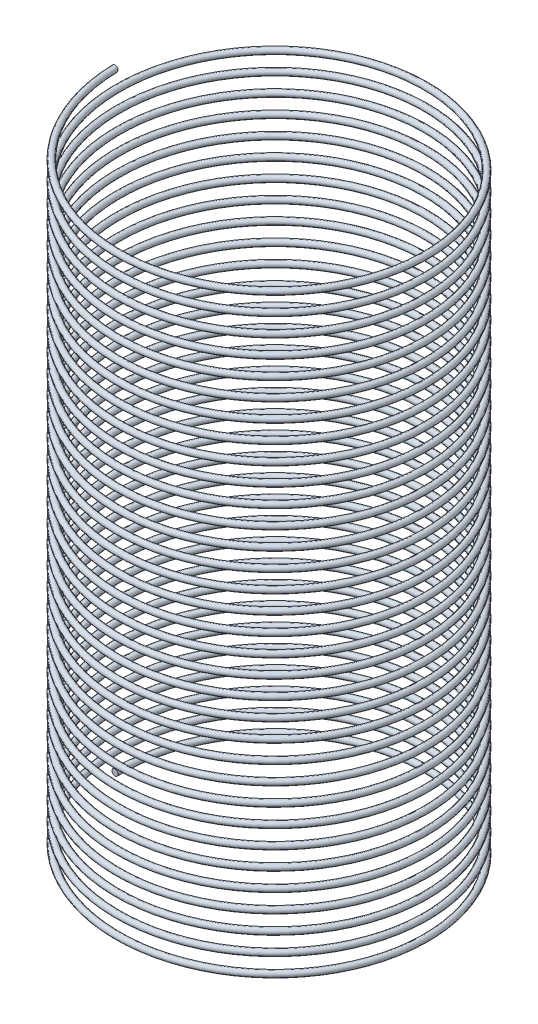
SolidWorks part; units mm, degrees
ref_plane "Front Plane" through (0, 0, 0) normal (0, 0, 1) x (1, 0, 0)
ref_plane "Top Plane" through (0, 0, 0) normal (0, 1, 0) x (1, 0, 0)
ref_plane "Right Plane" through (0, 0, 0) normal (1, 0, 0) x (0, 0, -1)
sketch "Sketch3" plane through (0, 0, 0) normal (0, 1, 0) x (1, 0, 0)
  circle A0 centre (0, 0) radius 25
  dimension "D1" = 50
curve "Helix/Spiral2" pitch 3 height 99 turns 33
sketch "Sketch4" plane through (0, 0, 0) normal (0, 0, 1) x (1, 0, 0)
  circle A0 centre (-25, 0) radius 0.5
  spline S0 degree 3 poles (-25, 0) (-25, 0.0451) (-24.3232, 0.1357) (-21.3588, 0.2712) (-16.6829, 0.4069) (-10.67, 0.5425) (-3.8022, 0.6781) (3.3704, 0.8137) (10.2728, 0.9493) (16.3521, 1.0849) (21.121, 1.2205) (24.1973, 1.3562) (25.3347, 1.4918) (24.4418, 1.6274) (21.5903, 1.763) (17.0087, 1.8986) (11.064, 2.0342) (4.2328, 2.1699) (-2.9376, 2.3055) (-9.8726, 2.4411) (-16.0165, 2.5767) (-20.8769, 2.7123) (-24.0643, 2.8479) (-25.3234, 2.9836) (-24.5532, 3.1192) (-21.8154, 3.2548) (-17.3294, 3.3904) (-11.4548, 3.526) (-4.6622, 3.6616) (2.5039, 3.7973) (9.4695, 3.9329) (15.6762, 4.0685) (20.6266, 4.2041) (23.9242, 4.3397) (25.3046, 4.4753) (24.6573, 4.611) (22.034, 4.7466) (17.6451, 4.8822) (11.8421, 5.0178) (5.0902, 5.1534) (-2.0696, 5.289) (-9.0635, 5.4247) (-15.3312, 5.5603) (-20.3703, 5.6959) (-23.777, 5.8315) (-25.2784, 5.9671) (-24.7541, 6.1027) (-22.2461, 6.2384) (-17.9555, 6.374) (-12.226, 6.5096) (-5.5168, 6.6452) (1.6345, 6.7808) (8.6549, 6.9164) (14.9816, 7.0521) (20.1078, 7.1877) (23.6227, 7.3233) (25.2446, 7.4589) (24.8435, 7.5945) (22.4516, 7.7301) (18.2606, 7.8658) (12.6062, 8.0014) (5.9416, 8.137) (-1.199, 8.2726) (-8.2437, 8.4082) (-14.6277, 8.5438) (-19.8395, 8.6795) (-23.4615, 8.8151) (-25.2034, 8.9507) (-24.9256, 9.0863) (-22.6505, 9.2219) (-18.5602, 9.3575) (-12.9827, 9.4932) (-6.3648, 9.6288) (0.7632, 9.7644) (7.83, 9.9) (14.2693, 10.0356) (19.5652, 10.1712) (23.2932, 10.3068) (25.1547, 10.4425) (25.0003, 10.5781) (22.8426, 10.7137) (18.8544, 10.8493) (13.3553, 10.9849) (6.786, 11.1205) (-0.3271, 11.2562) (-7.414, 11.3918) (-13.9068, 11.5274) (-19.2852, 11.663) (-23.1181, 11.7986) (-25.0985, 11.9342) (-25.0677, 12.0699) (-23.028, 12.2055) (-19.143, 12.3411) (-13.724, 12.4767) (-7.2052, 12.6123) (-0.109, 12.7479) (6.9959, 12.8836) (13.5402, 13.0192) (18.9994, 13.1548) (22.9362, 13.2904) (25.0349, 13.426) (25.1275, 13.5616) (23.2065, 13.6973) (19.4259, 13.8329) (14.0886, 13.9685) (7.6223, 14.1041) (0.5452, 14.2397) (-6.5756, 14.3753) (-13.1695, 14.511) (-18.708, 14.6466) (-22.7474, 14.7822) (-24.9639, 14.9178) (-25.18, 15.0534) (-23.3782, 15.189) (-19.7031, 15.3247) (-14.449, 15.4603) (-8.0371, 15.5959) (-0.9812, 15.7315) (6.1534, 15.8671) (12.7949, 16.0027) (18.4111, 16.1384) (22.5519, 16.274) (24.8855, 16.4096) (25.2249, 16.5452) (23.543, 16.6808) (19.9744, 16.8164) (14.8052, 16.9521) (8.4496, 17.0877) (1.4168, 17.2233) (-5.7294, 17.3589) (-12.4165, 17.4945) (-18.1087, 17.6301) (-22.3497, 17.7658) (-24.7997, 17.9014) (-25.2624, 18.037) (-23.7007, 18.1726) (-20.2398, 18.3082) (-15.157, 18.4438) (-8.8595, 18.5795) (-1.8521, 18.7151) (5.3037, 18.8507) (12.0345, 18.9863) (17.8009, 19.1219) (22.1409, 19.2575) (24.7066, 19.3932) (25.2924, 19.5288) (23.8515, 19.6644) (20.4992, 19.8) (15.5042, 19.9356) (9.2668, 20.0712) (2.2868, 20.2068) (-4.8764, 20.3425) (-11.6489, 20.4781) (-17.4879, 20.6137) (-21.9255, 20.7493) (-24.6061, 20.8849) (-25.315, 21.0205) (-23.9952, 21.1562) (-20.7525, 21.2918) (-15.8469, 21.4274) (-9.6714, 21.563) (-2.7209, 21.6986) (4.4477, 21.8342) (11.2598, 21.9699) (17.1697, 22.1055) (21.7036, 22.2411) (24.4984, 22.3767) (25.33, 22.5123) (24.1317, 22.6479) (20.9997, 22.7836) (16.1849, 22.9192) (10.0731, 23.0548) (3.1541, 23.1904) (-4.0176, 23.326) (-10.8674, 23.4616) (-16.8464, 23.5973) (-21.4753, 23.7329) (-24.3834, 23.8685) (-25.3375, 24.0041) (-24.2612, 24.1397) (-21.2407, 24.2753) (-16.5181, 24.411) (-10.4718, 24.5466) (-3.5864, 24.6822) (3.5864, 24.8178) (10.4718, 24.9534) (16.5181, 25.089) (21.2407, 25.2247) (24.2612, 25.3603) (25.3375, 25.4959) (24.3834, 25.6315) (21.4753, 25.7671) (16.8464, 25.9027) (10.8674, 26.0384) (4.0176, 26.174) (-3.1541, 26.3096) (-10.0731, 26.4452) (-16.1849, 26.5808) (-20.9997, 26.7164) (-24.1317, 26.8521) (-25.33, 26.9877) (-24.4984, 27.1233) (-21.7036, 27.2589) (-17.1697, 27.3945) (-11.2598, 27.5301) (-4.4477, 27.6658) (2.7209, 27.8014) (9.6714, 27.937) (15.8469, 28.0726) (20.7525, 28.2082) (23.9952, 28.3438) (25.315, 28.4795) (24.6061, 28.6151) (21.9255, 28.7507) (17.4879, 28.8863) (11.6489, 29.0219) (4.8764, 29.1575) (-2.2868, 29.2932) (-9.2668, 29.4288) (-15.5042, 29.5644) (-20.4992, 29.7) (-23.8515, 29.8356) (-25.2924, 29.9712) (-24.7066, 30.1068) (-22.1409, 30.2425) (-17.8009, 30.3781) (-12.0345, 30.5137) (-5.3037, 30.6493) (1.8521, 30.7849) (8.8595, 30.9205) (15.157, 31.0562) (20.2398, 31.1918) (23.7007, 31.3274) (25.2624, 31.463) (24.7997, 31.5986) (22.3497, 31.7342) (18.1087, 31.8699) (12.4165, 32.0055) (5.7294, 32.1411) (-1.4168, 32.2767) (-8.4496, 32.4123) (-14.8052, 32.5479) (-19.9744, 32.6836) (-23.543, 32.8192) (-25.2249, 32.9548) (-24.8855, 33.0904) (-22.5519, 33.226) (-18.4111, 33.3616) (-12.7949, 33.4973) (-6.1534, 33.6329) (0.9812, 33.7685) (8.0371, 33.9041) (14.449, 34.0397) (19.7031, 34.1753) (23.3782, 34.311) (25.18, 34.4466) (24.9639, 34.5822) (22.7474, 34.7178) (18.708, 34.8534) (13.1695, 34.989) (6.5756, 35.1247) (-0.5452, 35.2603) (-7.6223, 35.3959) (-14.0886, 35.5315) (-19.4259, 35.6671) (-23.2065, 35.8027) (-25.1275, 35.9384) (-25.0349, 36.074) (-22.9362, 36.2096) (-18.9994, 36.3452) (-13.5402, 36.4808) (-6.9959, 36.6164) (0.109, 36.7521) (7.2052, 36.8877) (13.724, 37.0233) (19.143, 37.1589) (23.028, 37.2945) (25.0677, 37.4301) (25.0985, 37.5658) (23.1181, 37.7014) (19.2852, 37.837) (13.9068, 37.9726) (7.414, 38.1082) (0.3271, 38.2438) (-6.786, 38.3795) (-13.3553, 38.5151) (-18.8544, 38.6507) (-22.8426, 38.7863) (-25.0003, 38.9219) (-25.1547, 39.0575) (-23.2932, 39.1932) (-19.5652, 39.3288) (-14.2693, 39.4644) (-7.83, 39.6) (-0.7632, 39.7356) (6.3648, 39.8712) (12.9827, 40.0068) (18.5602, 40.1425) (22.6505, 40.2781) (24.9256, 40.4137) (25.2034, 40.5493) (23.4615, 40.6849) (19.8395, 40.8205) (14.6277, 40.9562) (8.2437, 41.0918) (1.199, 41.2274) (-5.9416, 41.363) (-12.6062, 41.4986) (-18.2606, 41.6342) (-22.4516, 41.7699) (-24.8435, 41.9055) (-25.2446, 42.0411) (-23.6227, 42.1767) (-20.1078, 42.3123) (-14.9816, 42.4479) (-8.6549, 42.5836) (-1.6345, 42.7192) (5.5168, 42.8548) (12.226, 42.9904) (17.9555, 43.126) (22.2461, 43.2616) (24.7541, 43.3973) (25.2784, 43.5329) (23.777, 43.6685) (20.3703, 43.8041) (15.3312, 43.9397) (9.0635, 44.0753) (2.0696, 44.211) (-5.0902, 44.3466) (-11.8421, 44.4822) (-17.6451, 44.6178) (-22.034, 44.7534) (-24.6573, 44.889) (-25.3046, 45.0247) (-23.9242, 45.1603) (-20.6266, 45.2959) (-15.6762, 45.4315) (-9.4695, 45.5671) (-2.5039, 45.7027) (4.6622, 45.8384) (11.4548, 45.974) (17.3294, 46.1096) (21.8154, 46.2452) (24.5532, 46.3808) (25.3234, 46.5164) (24.0643, 46.6521) (20.8769, 46.7877) (16.0165, 46.9233) (9.8726, 47.0589) (2.9376, 47.1945) (-4.2328, 47.3301) (-11.064, 47.4658) (-17.0087, 47.6014) (-21.5903, 47.737) (-24.4418, 47.8726) (-25.3347, 48.0082) (-24.1973, 48.1438) (-21.121, 48.2795) (-16.3521, 48.4151) (-10.2728, 48.5507) (-3.3704, 48.6863) (3.8022, 48.8219) (10.67, 48.9575) (16.6829, 49.0932) (21.3588, 49.2288) (24.3232, 49.3644) (25.3384, 49.5) (24.3232, 49.6356) (21.3588, 49.7712) (16.6829, 49.9068) (10.67, 50.0425) (3.8022, 50.1781) (-3.3704, 50.3137) (-10.2728, 50.4493) (-16.3521, 50.5849) (-21.121, 50.7205) (-24.1973, 50.8562) (-25.3347, 50.9918) (-24.4418, 51.1274) (-21.5903, 51.263) (-17.0087, 51.3986) (-11.064, 51.5342) (-4.2328, 51.6699) (2.9376, 51.8055) (9.8726, 51.9411) (16.0165, 52.0767) (20.8769, 52.2123) (24.0643, 52.3479) (25.3234, 52.4836) (24.5532, 52.6192) (21.8154, 52.7548) (17.3294, 52.8904) (11.4548, 53.026) (4.6622, 53.1616) (-2.5039, 53.2973) (-9.4695, 53.4329) (-15.6762, 53.5685) (-20.6266, 53.7041) (-23.9242, 53.8397) (-25.3046, 53.9753) (-24.6573, 54.111) (-22.034, 54.2466) (-17.6451, 54.3822) (-11.8421, 54.5178) (-5.0902, 54.6534) (2.0696, 54.789) (9.0635, 54.9247) (15.3312, 55.0603) (20.3703, 55.1959) (23.777, 55.3315) (25.2784, 55.4671) (24.7541, 55.6027) (22.2461, 55.7384) (17.9555, 55.874) (12.226, 56.0096) (5.5168, 56.1452) (-1.6345, 56.2808) (-8.6549, 56.4164) (-14.9816, 56.5521) (-20.1078, 56.6877) (-23.6227, 56.8233) (-25.2446, 56.9589) (-24.8435, 57.0945) (-22.4516, 57.2301) (-18.2606, 57.3658) (-12.6062, 57.5014) (-5.9416, 57.637) (1.199, 57.7726) (8.2437, 57.9082) (14.6277, 58.0438) (19.8395, 58.1795) (23.4615, 58.3151) (25.2034, 58.4507) (24.9256, 58.5863) (22.6505, 58.7219) (18.5602, 58.8575) (12.9827, 58.9932) (6.3648, 59.1288) (-0.7632, 59.2644) (-7.83, 59.4) (-14.2693, 59.5356) (-19.5652, 59.6712) (-23.2932, 59.8068) (-25.1547, 59.9425) (-25.0003, 60.0781) (-22.8426, 60.2137) (-18.8544, 60.3493) (-13.3553, 60.4849) (-6.786, 60.6205) (0.3271, 60.7562) (7.414, 60.8918) (13.9068, 61.0274) (19.2852, 61.163) (23.1181, 61.2986) (25.0985, 61.4342) (25.0677, 61.5699) (23.028, 61.7055) (19.143, 61.8411) (13.724, 61.9767) (7.2052, 62.1123) (0.109, 62.2479) (-6.9959, 62.3836) (-13.5402, 62.5192) (-18.9994, 62.6548) (-22.9362, 62.7904) (-25.0349, 62.926) (-25.1275, 63.0616) (-23.2065, 63.1973) (-19.4259, 63.3329) (-14.0886, 63.4685) (-7.6223, 63.6041) (-0.5452, 63.7397) (6.5756, 63.8753) (13.1695, 64.011) (18.708, 64.1466) (22.7474, 64.2822) (24.9639, 64.4178) (25.18, 64.5534) (23.3782, 64.689) (19.7031, 64.8247) (14.449, 64.9603) (8.0371, 65.0959) (0.9812, 65.2315) (-6.1534, 65.3671) (-12.7949, 65.5027) (-18.4111, 65.6384) (-22.5519, 65.774) (-24.8855, 65.9096) (-25.2249, 66.0452) (-23.543, 66.1808) (-19.9744, 66.3164) (-14.8052, 66.4521) (-8.4496, 66.5877) (-1.4168, 66.7233) (5.7294, 66.8589) (12.4165, 66.9945) (18.1087, 67.1301) (22.3497, 67.2658) (24.7997, 67.4014) (25.2624, 67.537) (23.7007, 67.6726) (20.2398, 67.8082) (15.157, 67.9438) (8.8595, 68.0795) (1.8521, 68.2151) (-5.3037, 68.3507) (-12.0345, 68.4863) (-17.8009, 68.6219) (-22.1409, 68.7575) (-24.7066, 68.8932) (-25.2924, 69.0288) (-23.8515, 69.1644) (-20.4992, 69.3) (-15.5042, 69.4356) (-9.2668, 69.5712) (-2.2868, 69.7068) (4.8764, 69.8425) (11.6489, 69.9781) (17.4879, 70.1137) (21.9255, 70.2493) (24.6061, 70.3849) (25.315, 70.5205) (23.9952, 70.6562) (20.7525, 70.7918) (15.8469, 70.9274) (9.6714, 71.063) (2.7209, 71.1986) (-4.4477, 71.3342) (-11.2598, 71.4699) (-17.1697, 71.6055) (-21.7036, 71.7411) (-24.4984, 71.8767) (-25.33, 72.0123) (-24.1317, 72.1479) (-20.9997, 72.2836) (-16.1849, 72.4192) (-10.0731, 72.5548) (-3.1541, 72.6904) (4.0176, 72.826) (10.8674, 72.9616) (16.8464, 73.0973) (21.4753, 73.2329) (24.3834, 73.3685) (25.3375, 73.5041) (24.2612, 73.6397) (21.2407, 73.7753) (16.5181, 73.911) (10.4718, 74.0466) (3.5864, 74.1822) (-3.5864, 74.3178) (-10.4718, 74.4534) (-16.5181, 74.589) (-21.2407, 74.7247) (-24.2612, 74.8603) (-25.3375, 74.9959) (-24.3834, 75.1315) (-21.4753, 75.2671) (-16.8464, 75.4027) (-10.8674, 75.5384) (-4.0176, 75.674) (3.1541, 75.8096) (10.0731, 75.9452) (16.1849, 76.0808) (20.9997, 76.2164) (24.1317, 76.3521) (25.33, 76.4877) (24.4984, 76.6233) (21.7036, 76.7589) (17.1697, 76.8945) (11.2598, 77.0301) (4.4477, 77.1658) (-2.7209, 77.3014) (-9.6714, 77.437) (-15.8469, 77.5726) (-20.7525, 77.7082) (-23.9952, 77.8438) (-25.315, 77.9795) (-24.6061, 78.1151) (-21.9255, 78.2507) (-17.4879, 78.3863) (-11.6489, 78.5219) (-4.8764, 78.6575) (2.2868, 78.7932) (9.2668, 78.9288) (15.5042, 79.0644) (20.4992, 79.2) (23.8515, 79.3356) (25.2924, 79.4712) (24.7066, 79.6068) (22.1409, 79.7425) (17.8009, 79.8781) (12.0345, 80.0137) (5.3037, 80.1493) (-1.8521, 80.2849) (-8.8595, 80.4205) (-15.157, 80.5562) (-20.2398, 80.6918) (-23.7007, 80.8274) (-25.2624, 80.963) (-24.7997, 81.0986) (-22.3497, 81.2342) (-18.1087, 81.3699) (-12.4165, 81.5055) (-5.7294, 81.6411) (1.4168, 81.7767) (8.4496, 81.9123) (14.8052, 82.0479) (19.9744, 82.1836) (23.543, 82.3192) (25.2249, 82.4548) (24.8855, 82.5904) (22.5519, 82.726) (18.4111, 82.8616) (12.7949, 82.9973) (6.1534, 83.1329) (-0.9812, 83.2685) (-8.0371, 83.4041) (-14.449, 83.5397) (-19.7031, 83.6753) (-23.3782, 83.811) (-25.18, 83.9466) (-24.9639, 84.0822) (-22.7474, 84.2178) (-18.708, 84.3534) (-13.1695, 84.489) (-6.5756, 84.6247) (0.5452, 84.7603) (7.6223, 84.8959) (14.0886, 85.0315) (19.4259, 85.1671) (23.2065, 85.3027) (25.1275, 85.4384) (25.0349, 85.574) (22.9362, 85.7096) (18.9994, 85.8452) (13.5402, 85.9808) (6.9959, 86.1164) (-0.109, 86.2521) (-7.2052, 86.3877) (-13.724, 86.5233) (-19.143, 86.6589) (-23.028, 86.7945) (-25.0677, 86.9301) (-25.0985, 87.0658) (-23.1181, 87.2014) (-19.2852, 87.337) (-13.9068, 87.4726) (-7.414, 87.6082) (-0.3271, 87.7438) (6.786, 87.8795) (13.3553, 88.0151) (18.8544, 88.1507) (22.8426, 88.2863) (25.0003, 88.4219) (25.1547, 88.5575) (23.2932, 88.6932) (19.5652, 88.8288) (14.2693, 88.9644) (7.83, 89.1) (0.7632, 89.2356) (-6.3648, 89.3712) (-12.9827, 89.5068) (-18.5602, 89.6425) (-22.6505, 89.7781) (-24.9256, 89.9137) (-25.2034, 90.0493) (-23.4615, 90.1849) (-19.8395, 90.3205) (-14.6277, 90.4562) (-8.2437, 90.5918) (-1.199, 90.7274) (5.9416, 90.863) (12.6062, 90.9986) (18.2606, 91.1342) (22.4516, 91.2699) (24.8435, 91.4055) (25.2446, 91.5411) (23.6227, 91.6767) (20.1078, 91.8123) (14.9816, 91.9479) (8.6549, 92.0836) (1.6345, 92.2192) (-5.5168, 92.3548) (-12.226, 92.4904) (-17.9555, 92.626) (-22.2461, 92.7616) (-24.7541, 92.8973) (-25.2784, 93.0329) (-23.777, 93.1685) (-20.3703, 93.3041) (-15.3312, 93.4397) (-9.0635, 93.5753) (-2.0696, 93.711) (5.0902, 93.8466) (11.8421, 93.9822) (17.6451, 94.1178) (22.034, 94.2534) (24.6573, 94.389) (25.3046, 94.5247) (23.9242, 94.6603) (20.6266, 94.7959) (15.6762, 94.9315) (9.4695, 95.0671) (2.5039, 95.2027) (-4.6622, 95.3384) (-11.4548, 95.474) (-17.3294, 95.6096) (-21.8154, 95.7452) (-24.5532, 95.8808) (-25.3234, 96.0164) (-24.0643, 96.1521) (-20.8769, 96.2877) (-16.0165, 96.4233) (-9.8726, 96.5589) (-2.9376, 96.6945) (4.2328, 96.8301) (11.064, 96.9658) (17.0087, 97.1014) (21.5903, 97.237) (24.4418, 97.3726) (25.3347, 97.5082) (24.1973, 97.6438) (21.121, 97.7795) (16.3521, 97.9151) (10.2728, 98.0507) (3.3704, 98.1863) (-3.8022, 98.3219) (-10.67, 98.4575) (-16.6829, 98.5931) (-21.3588, 98.7288) (-24.3232, 98.8643) (-25, 98.9549) (-25, 99) knots 0 0 0 0 0.00137 0.00274 0.00411 0.005479 0.006849 0.008219 0.009589 0.010959 0.012329 0.013699 0.015068 0.016438 0.017808 0.019178 0.020548 0.021918 0.023288 0.024658 0.026027 0.027397 0.028767 0.030137 0.031507 0.032877 0.034247 0.035616 0.036986 0.038356 0.039726 0.041096 0.042466 0.043836 0.045205 0.046575 0.047945 0.049315 0.050685 0.052055 0.053425 0.054795 0.056164 0.057534 0.058904 0.060274 0.061644 0.063014 0.064384 0.065753 0.067123 0.068493 0.069863 0.071233 0.072603 0.073973 0.075342 0.076712 0.078082 0.079452 0.080822 0.082192 0.083562 0.084932 0.086301 0.087671 0.089041 0.090411 0.091781 0.093151 0.094521 0.09589 0.09726 0.09863 0.1 0.10137 0.10274 0.10411 0.105479 0.106849 0.108219 0.109589 0.110959 0.112329 0.113699 0.115068 0.116438 0.117808 0.119178 0.120548 0.121918 0.123288 0.124658 0.126027 0.127397 0.128767 0.130137 0.131507 0.132877 0.134247 0.135616 0.136986 0.138356 0.139726 0.141096 0.142466 0.143836 0.145205 0.146575 0.147945 0.149315 0.150685 0.152055 0.153425 0.154795 0.156164 0.157534 0.158904 0.160274 0.161644 0.163014 0.164384 0.165753 0.167123 0.168493 0.169863 0.171233 0.172603 0.173973 0.175342 0.176712 0.178082 0.179452 0.180822 0.182192 0.183562 0.184932 0.186301 0.187671 0.189041 0.190411 0.191781 0.193151 0.194521 0.19589 0.19726 0.19863 0.2 0.20137 0.20274 0.20411 0.205479 0.206849 0.208219 0.209589 0.210959 0.212329 0.213699 0.215068 0.216438 0.217808 0.219178 0.220548 0.221918 0.223288 0.224658 0.226027 0.227397 0.228767 0.230137 0.231507 0.232877 0.234247 0.235616 0.236986 0.238356 0.239726 0.241096 0.242466 0.243836 0.245205 0.246575 0.247945 0.249315 0.250685 0.252055 0.253425 0.254795 0.256164 0.257534 0.258904 0.260274 0.261644 0.263014 0.264384 0.265753 0.267123 0.268493 0.269863 0.271233 0.272603 0.273973 0.275342 0.276712 0.278082 0.279452 0.280822 0.282192 0.283562 0.284932 0.286301 0.287671 0.289041 0.290411 0.291781 0.293151 0.294521 0.29589 0.29726 0.29863 0.3 0.30137 0.30274 0.30411 0.305479 0.306849 0.308219 0.309589 0.310959 0.312329 0.313699 0.315068 0.316438 0.317808 0.319178 0.320548 0.321918 0.323288 0.324658 0.326027 0.327397 0.328767 0.330137 0.331507 0.332877 0.334247 0.335616 0.336986 0.338356 0.339726 0.341096 0.342466 0.343836 0.345205 0.346575 0.347945 0.349315 0.350685 0.352055 0.353425 0.354795 0.356164 0.357534 0.358904 0.360274 0.361644 0.363014 0.364384 0.365753 0.367123 0.368493 0.369863 0.371233 0.372603 0.373973 0.375342 0.376712 0.378082 0.379452 0.380822 0.382192 0.383562 0.384932 0.386301 0.387671 0.389041 0.390411 0.391781 0.393151 0.394521 0.39589 0.39726 0.39863 0.4 0.40137 0.40274 0.40411 0.405479 0.406849 0.408219 0.409589 0.410959 0.412329 0.413699 0.415068 0.416438 0.417808 0.419178 0.420548 0.421918 0.423288 0.424658 0.426027 0.427397 0.428767 0.430137 0.431507 0.432877 0.434247 0.435616 0.436986 0.438356 0.439726 0.441096 0.442466 0.443836 0.445205 0.446575 0.447945 0.449315 0.450685 0.452055 0.453425 0.454795 0.456164 0.457534 0.458904 0.460274 0.461644 0.463014 0.464384 0.465753 0.467123 0.468493 0.469863 0.471233 0.472603 0.473973 0.475342 0.476712 0.478082 0.479452 0.480822 0.482192 0.483562 0.484932 0.486301 0.487671 0.489041 0.490411 0.491781 0.493151 0.494521 0.49589 0.49726 0.49863 0.5 0.50137 0.50274 0.50411 0.505479 0.506849 0.508219 0.509589 0.510959 0.512329 0.513699 0.515068 0.516438 0.517808 0.519178 0.520548 0.521918 0.523288 0.524658 0.526027 0.527397 0.528767 0.530137 0.531507 0.532877 0.534247 0.535616 0.536986 0.538356 0.539726 0.541096 0.542466 0.543836 0.545205 0.546575 0.547945 0.549315 0.550685 0.552055 0.553425 0.554795 0.556164 0.557534 0.558904 0.560274 0.561644 0.563014 0.564384 0.565753 0.567123 0.568493 0.569863 0.571233 0.572603 0.573973 0.575342 0.576712 0.578082 0.579452 0.580822 0.582192 0.583562 0.584932 0.586301 0.587671 0.589041 0.590411 0.591781 0.593151 0.594521 0.59589 0.59726 0.59863 0.6 0.60137 0.60274 0.60411 0.605479 0.606849 0.608219 0.609589 0.610959 0.612329 0.613699 0.615068 0.616438 0.617808 0.619178 0.620548 0.621918 0.623288 0.624658 0.626027 0.627397 0.628767 0.630137 0.631507 0.632877 0.634247 0.635616 0.636986 0.638356 0.639726 0.641096 0.642466 0.643836 0.645205 0.646575 0.647945 0.649315 0.650685 0.652055 0.653425 0.654795 0.656164 0.657534 0.658904 0.660274 0.661644 0.663014 0.664384 0.665753 0.667123 0.668493 0.669863 0.671233 0.672603 0.673973 0.675342 0.676712 0.678082 0.679452 0.680822 0.682192 0.683562 0.684932 0.686301 0.687671 0.689041 0.690411 0.691781 0.693151 0.694521 0.69589 0.69726 0.69863 0.7 0.70137 0.70274 0.70411 0.705479 0.706849 0.708219 0.709589 0.710959 0.712329 0.713699 0.715068 0.716438 0.717808 0.719178 0.720548 0.721918 0.723288 0.724658 0.726027 0.727397 0.728767 0.730137 0.731507 0.732877 0.734247 0.735616 0.736986 0.738356 0.739726 0.741096 0.742466 0.743836 0.745205 0.746575 0.747945 0.749315 0.750685 0.752055 0.753425 0.754795 0.756164 0.757534 0.758904 0.760274 0.761644 0.763014 0.764384 0.765753 0.767123 0.768493 0.769863 0.771233 0.772603 0.773973 0.775342 0.776712 0.778082 0.779452 0.780822 0.782192 0.783562 0.784932 0.786301 0.787671 0.789041 0.790411 0.791781 0.793151 0.794521 0.79589 0.79726 0.79863 0.8 0.80137 0.80274 0.80411 0.805479 0.806849 0.808219 0.809589 0.810959 0.812329 0.813699 0.815068 0.816438 0.817808 0.819178 0.820548 0.821918 0.823288 0.824658 0.826027 0.827397 0.828767 0.830137 0.831507 0.832877 0.834247 0.835616 0.836986 0.838356 0.839726 0.841096 0.842466 0.843836 0.845205 0.846575 0.847945 0.849315 0.850685 0.852055 0.853425 0.854795 0.856164 0.857534 0.858904 0.860274 0.861644 0.863014 0.864384 0.865753 0.867123 0.868493 0.869863 0.871233 0.872603 0.873973 0.875342 0.876712 0.878082 0.879452 0.880822 0.882192 0.883562 0.884932 0.886301 0.887671 0.889041 0.890411 0.891781 0.893151 0.894521 0.89589 0.89726 0.89863 0.9 0.90137 0.90274 0.90411 0.905479 0.906849 0.908219 0.909589 0.910959 0.912329 0.913699 0.915068 0.916438 0.917808 0.919178 0.920548 0.921918 0.923288 0.924658 0.926027 0.927397 0.928767 0.930137 0.931507 0.932877 0.934247 0.935616 0.936986 0.938356 0.939726 0.941096 0.942466 0.943836 0.945205 0.946575 0.947945 0.949315 0.950685 0.952055 0.953425 0.954795 0.956164 0.957534 0.958904 0.960274 0.961644 0.963014 0.964384 0.965753 0.967123 0.968493 0.969863 0.971233 0.972603 0.973973 0.975342 0.976712 0.978082 0.979452 0.980822 0.982192 0.983562 0.984932 0.986301 0.987671 0.989041 0.990411 0.991781 0.993151 0.994521 0.99589 0.99726 0.99863 1 1 1 1 construction
  point P2 (0, 0)
  point P3 (0, 0)
  point P6 (0, 0)
  dimension "D1" = 1
sweep "Sweep1" add profiles "Sketch4" path "Helix/Spiral2"
